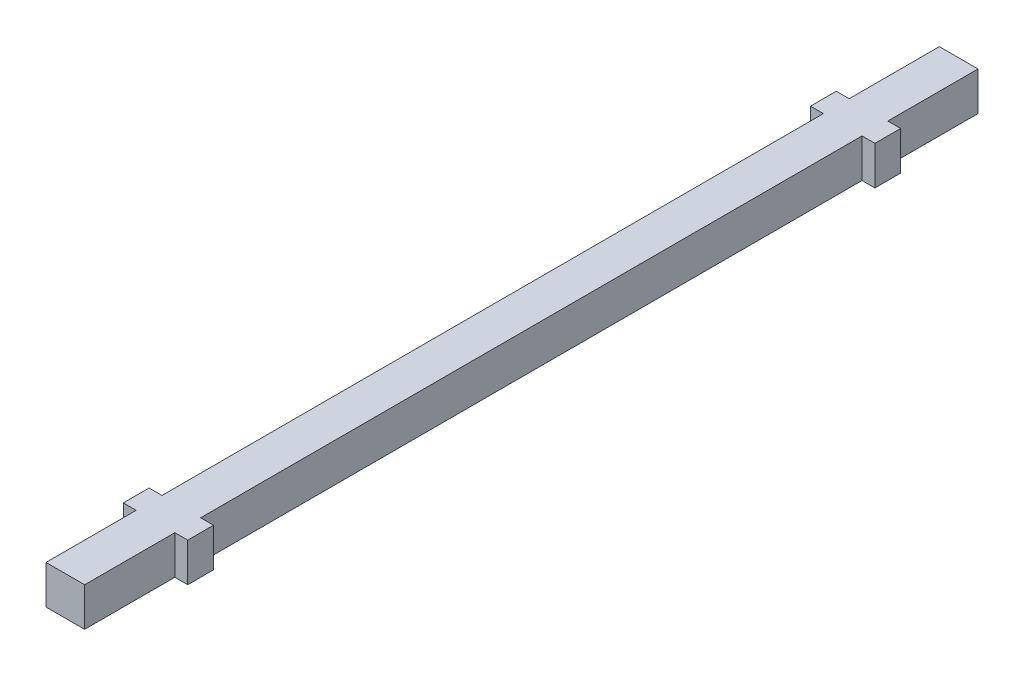
SolidWorks part; units mm, degrees
ref_plane "Front Plane" through (0, 0, 0) normal (0, 0, 1) x (1, 0, 0)
ref_plane "Top Plane" through (0, 0, 0) normal (0, 1, 0) x (1, 0, 0)
ref_plane "Right Plane" through (0, 0, 0) normal (1, 0, 0) x (0, 0, -1)
sketch "Sketch1" plane through (0, 0, 0) normal (0, 0, 1) x (1, 0, 0)
  line L1 (-4.5, -4.5) -> (4.5, -4.5)
  line L2 (-4.5, -4.5) -> (-4.5, 4.5)
  line L3 (-4.5, 4.5) -> (4.5, 4.5)
  line L4 (4.5, -4.5) -> (4.5, 4.5)
  line L5 (-4.5, -4.5) -> (4.5, 4.5) construction
  line L6 (-4.5, 4.5) -> (4.5, -4.5) construction
  point P0 (0, 0)
  dimension "D1" = 9
extrude "Boss-Extrude1" add sketch "Sketch1" along normal mid plane 208
sketch "Sketch2" plane through (0, 0, 0) normal (0, 1, 0) x (1, 0, 0)
  line L0 (4.5, -104) -> (4.5, 104) construction
  line L1 (4.5, 83) -> (7.5, 83)
  line L2 (4.5, 83) -> (4.5, -83)
  line L3 (4.5, -83) -> (7.5, -83)
  line L4 (7.5, 83) -> (7.5, -83)
  line L5 (-4.5, -104) -> (-4.5, 104) construction
  line L6 (-4.5, 83) -> (-7.5, 83)
  line L7 (-4.5, 83) -> (-4.5, -83)
  line L8 (-4.5, -83) -> (-7.5, -83)
  line L9 (-7.5, 83) -> (-7.5, -83)
  line L10 (7.5, 77) -> (4.5, 77)
  line L11 (-4.5, 77) -> (-7.5, 77)
  line L12 (-7.5, -77) -> (-4.5, -77)
  line L13 (4.5, -77) -> (7.5, -77)
  point P12 (7.5, 0)
  dimension "D1" = 3
  dimension "D2" = 166
  dimension "D3" = 6
  dimension "D4" = 6
extrude "Boss-Extrude2" add sketch "Sketch2" along normal mid plane 9 contours L12 L9 L8 L7 | L13 L2 L3 L4 | L10 L4 L1 L2 | L11 L7 L6 L9
